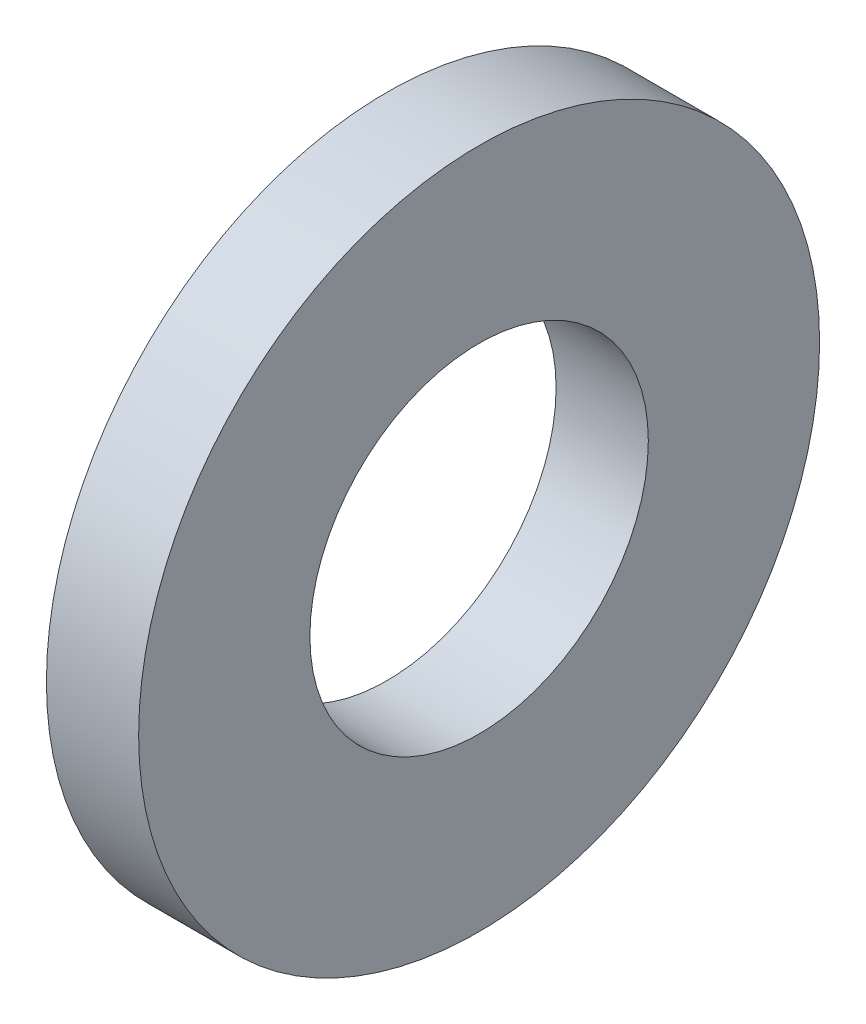
SolidWorks part; units mm, degrees
ref_plane "Front Plane" through (0, 0, 0) normal (0, 0, 1) x (1, 0, 0)
ref_plane "Top Plane" through (0, 0, 0) normal (0, 1, 0) x (1, 0, 0)
ref_plane "Right Plane" through (0, 0, 0) normal (1, 0, 0) x (0, 0, -1)
sketch "Sketch1" plane through (0, 0, 0) normal (1, 0, 0) x (0, 0, -1)
  circle A0 centre (0, 0) radius 10.5029
  circle A1 centre (0, 0) radius 5.2197
  dimension "OD" = 21.0058
  dimension "ID" = 10.4394
extrude "Boss-Extrude1" add sketch "Sketch1" along normal blind 2.8448
